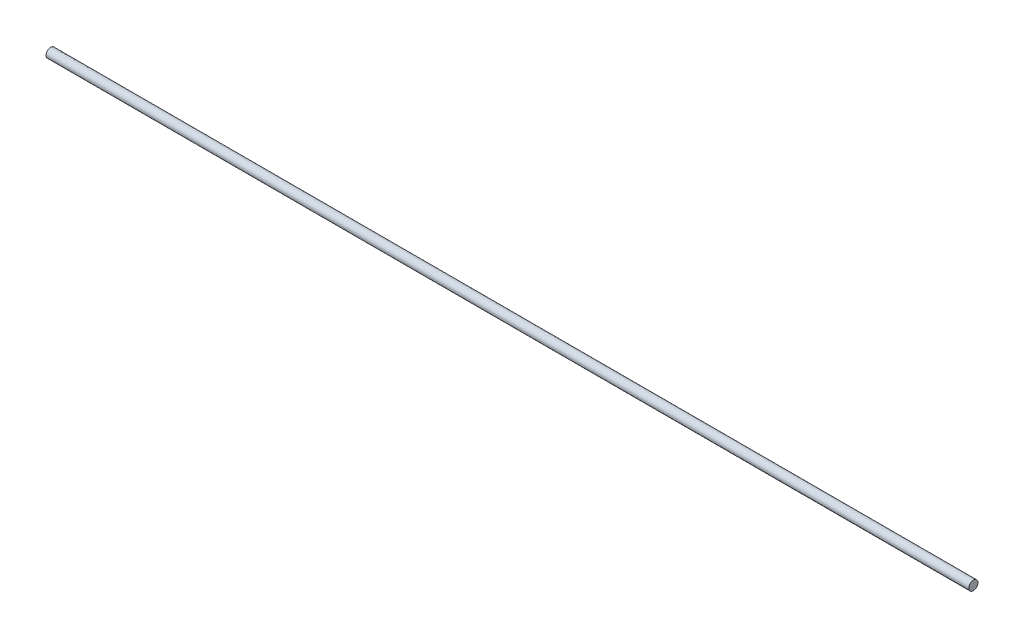
SolidWorks part; units mm, degrees
ref_plane "前视基准面" through (0, 0, 0) normal (0, 0, 1) x (1, 0, 0)
ref_plane "上视基准面" through (0, 0, 0) normal (0, 1, 0) x (1, 0, 0)
ref_plane "右视基准面" through (0, 0, 0) normal (1, 0, 0) x (0, 0, -1)
sketch "草图1" plane through (0, 0, 0) normal (1, 0, 0) x (0, 0, -1)
  circle A0 centre (0, 0) radius 0.5
  dimension "D1" = 1
extrude "凸台-拉伸1" add sketch "草图1" along normal blind 100
